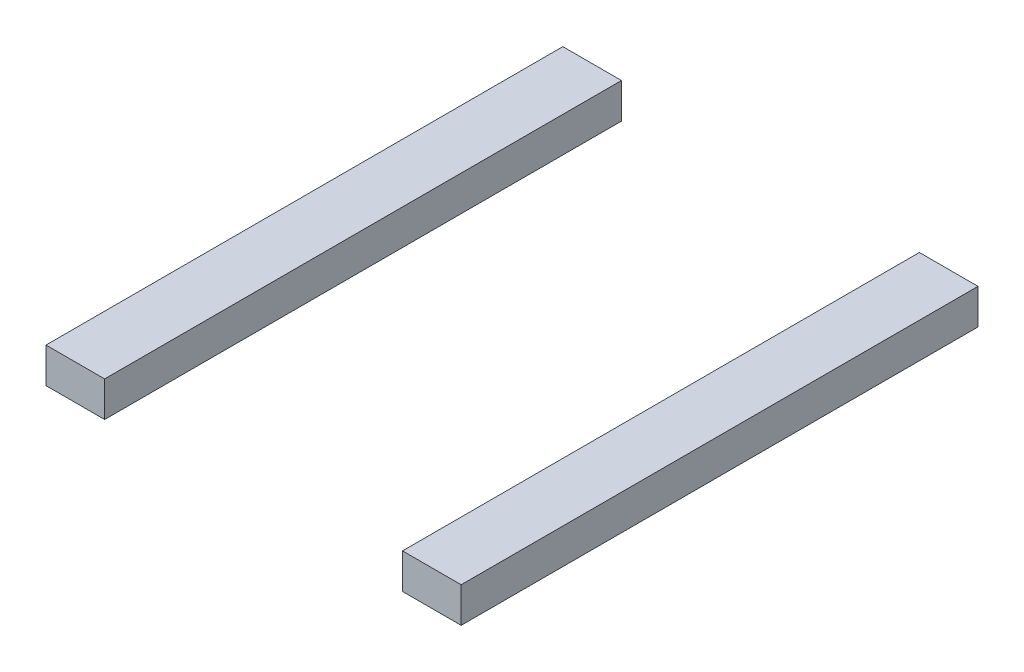
SolidWorks part; units mm, degrees
ref_plane "Спереди" through (0, 0, 0) normal (0, 0, 1) x (1, 0, 0)
ref_plane "Сверху" through (0, 0, 0) normal (0, 1, 0) x (1, 0, 0)
ref_plane "Справа" through (0, 0, 0) normal (1, 0, 0) x (0, 0, -1)
sketch "Эскиз1" plane through (0, 0, 0) normal (0, 1, 0) x (1, 0, 0)
  line L0 (-77.036, 0) -> (-76.536, 0)
  line L1 (-76.536, 0) -> (-76.536, -4.4071)
  line L2 (-76.536, -4.4071) -> (-77.036, -4.4071)
  line L3 (-77.036, -4.4071) -> (-77.036, 0)
  line L4 (-73.996, 0) -> (-73.996, -4.4071)
  line L5 (-73.996, 0) -> (-73.496, 0)
  line L6 (-73.496, 0) -> (-73.496, -4.4071)
  line L7 (-73.496, -4.4071) -> (-73.996, -4.4071)
  dimension "D1" = 2.54
  dimension "D2" = 0.5
  dimension "D3" = 0.5
extrude "Бобышка-Вытянуть1" add sketch "Эскиз1" along normal blind 0.3
sketch "Эскиз2" plane through (0, 0, 4.4071) normal (0, 0, -1) x (-1, 0, 0)
  line L0 (73.996, 0) -> (73.996, 0.3) construction
  line L1 (73.8811, 0.15) -> (76.6336, 0.15) construction
